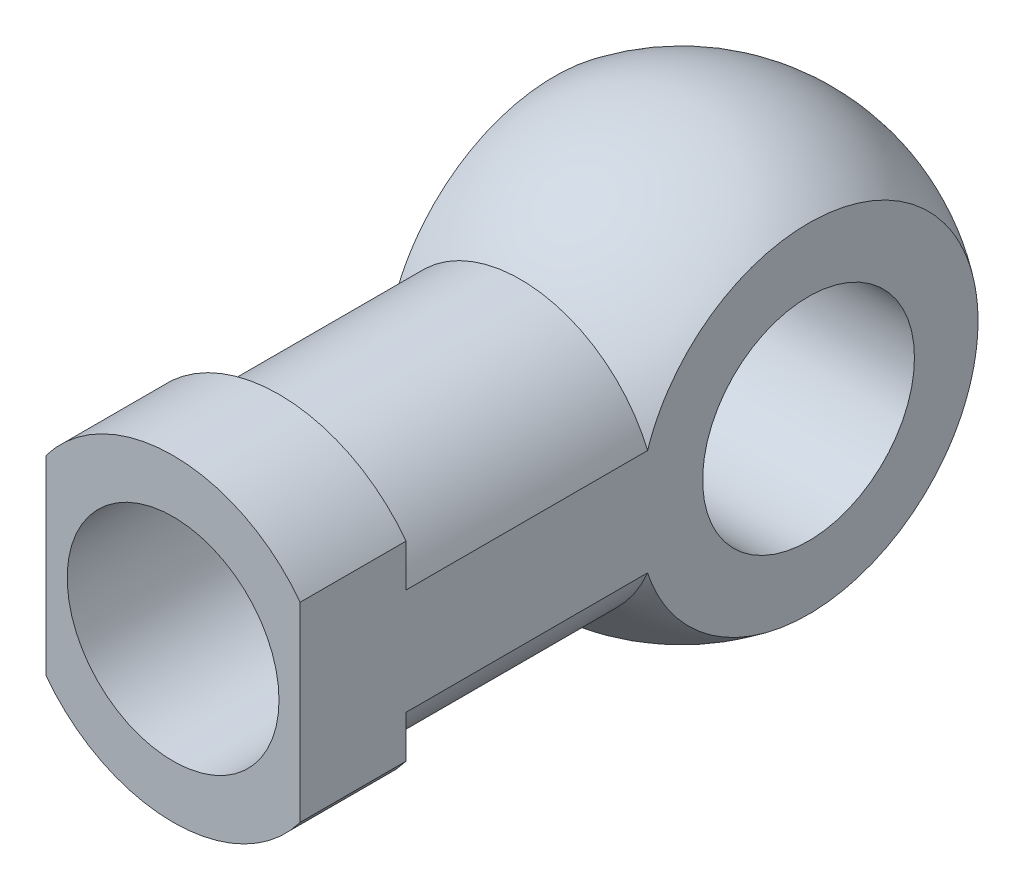
SolidWorks part; units mm, degrees
ref_plane "Front Plane" through (0, 0, 0) normal (0, 0, 1) x (1, 0, 0)
ref_plane "Top Plane" through (0, 0, 0) normal (0, 1, 0) x (1, 0, 0)
ref_plane "Right Plane" through (0, 0, 0) normal (1, 0, 0) x (0, 0, -1)
sketch "Sketch1" plane through (0, 0, 0) normal (0, 0, 1) x (1, 0, 0)
  circle A0 centre (0, 0) radius 7.5
  circle A1 centre (0, 0) radius 5
  dimension "D1" = 10
  dimension "D2" = 15
extrude "Boss-Extrude1" add sketch "Sketch1" along normal blind 5
sketch "Sketch2" plane through (0, 0, 0) normal (0, 0, -1) x (-1, 0, 0)
  circle A0 centre (0, 0) radius 6.5
  dimension "D1" = 13
extrude "Boss-Extrude2" add sketch "Sketch2" along normal blind 19
sketch "Sketch3" plane through (0, 0, 0) normal (0, 1, 0) x (1, 0, 0)
  line L0 (6.5, 19) -> (-6.5, 19) construction
  line L1 (0, 19) -> (0, 29) construction
  line L2 (0, 29) -> (0, 9) construction
  line L3 (0, 29) -> (0, 9)
  arc A0 (0, 29) -> (0, 9) centre (0, 19) ccw
  dimension "D1" = 20
revolve "Revolve9" add sketch "Sketch3" angle 360 about L3
sketch "Sketch4" plane through (0, 0, 5) normal (0, 0, 1) x (1, 0, 0)
  line L1 (-6, -10.6812) -> (6, -10.6812)
  line L2 (-6, -10.6812) -> (-6, 10.6812)
  line L3 (-6, 10.6812) -> (6, 10.6812)
  line L4 (6, -10.6812) -> (6, 10.6812)
  line L5 (-6, -10.6812) -> (6, 10.6812) construction
  line L6 (-6, 10.6812) -> (6, -10.6812) construction
  line L7 (-10.8744, -15.385) -> (10.8744, -15.385)
  line L8 (-10.8744, -15.385) -> (-10.8744, 15.385)
  line L9 (-10.8744, 15.385) -> (10.8744, 15.385)
  line L10 (10.8744, -15.385) -> (10.8744, 15.385)
  line L11 (-10.8744, -15.385) -> (10.8744, 15.385) construction
  line L12 (-10.8744, 15.385) -> (10.8744, -15.385) construction
  point P0 (0, 0)
  point P6 (0, 0)
  dimension "D1" = 12
extrude "Cut-Extrude1" cut sketch "Sketch4" against normal blind 38
sketch "Sketch5" plane through (0, 0, 0) normal (0, 0, 1) x (1, 0, 0)
  circle A0 centre (0, 0) radius 5
extrude "Cut-Extrude2" cut sketch "Sketch5" against normal blind 5
sketch "Sketch6" plane through (6, 0, 0) normal (1, 0, 0) x (0, 0, -1)
  circle A0 centre (19, 0) radius 5
  dimension "D1" = 10
extrude "Cut-Extrude3" cut sketch "Sketch6" against normal blind 37
